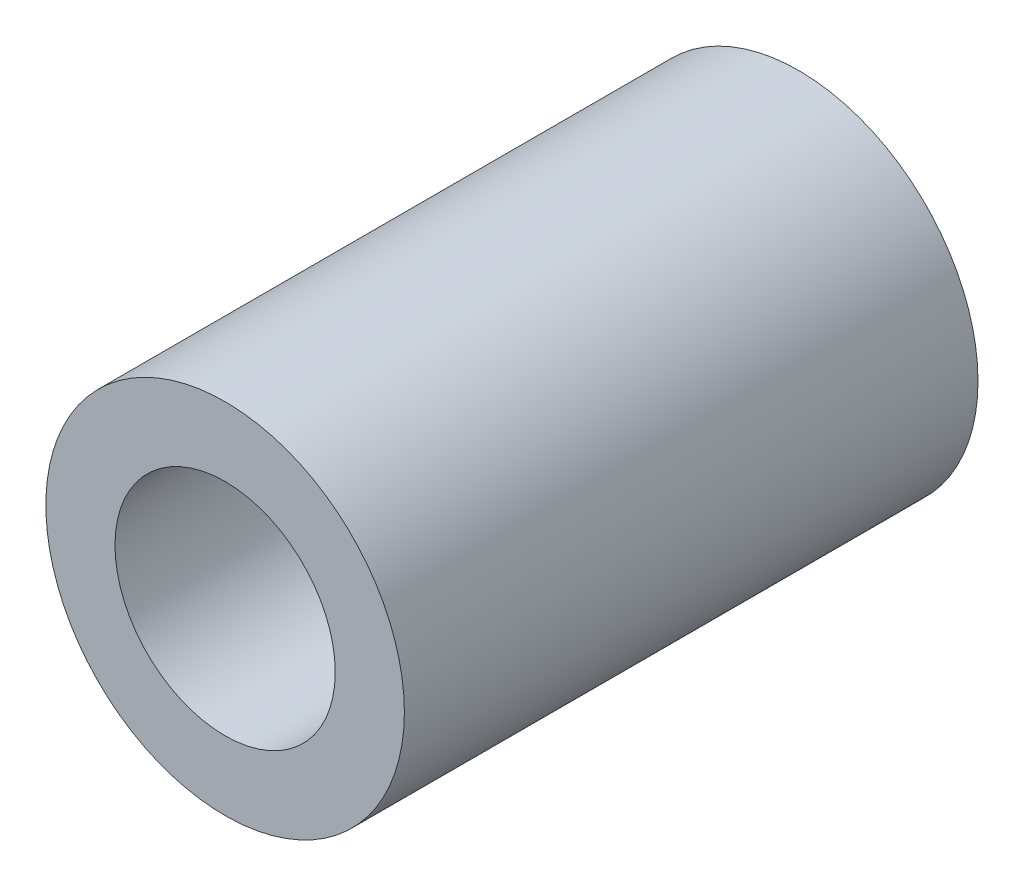
SolidWorks part; units mm, degrees
ref_plane "Front Plane" through (0, 0, 0) normal (0, 0, 1) x (1, 0, 0)
ref_plane "Top Plane" through (0, 0, 0) normal (0, 1, 0) x (1, 0, 0)
ref_plane "Right Plane" through (0, 0, 0) normal (1, 0, 0) x (0, 0, -1)
sketch "Sketch1" plane through (0, 0, 0) normal (0, 0, 1) x (1, 0, 0)
  line L0 (0, 2.4384) -> (0, 3.9688) construction
  line L1 (0, -2.4384) -> (0, -3.9688) construction
  circle A0 centre (0, 0) radius 3.9688
  circle A1 centre (0, 0) radius 2.4384
  dimension "OD" = 7.9375
  dimension "ID" = 4.8768
sketch "Sketch2" plane through (0, 0, 0) normal (1, 0, 0) x (0, 0, -1)
  line L0 (-6.35, 2.4384) -> (6.35, 2.4384) construction
  line L1 (-6.35, -2.4384) -> (6.35, -2.4384) construction
  line L2 (-6.35, -3.9688) -> (6.35, -3.9688) construction
  line L3 (-6.35, 3.9688) -> (6.35, 3.9688) construction
  dimension "Length" = 12.7
extrude "Extrude1" add sketch "Sketch1" along normal up to vertex (6.35 mm away) and the other way up to vertex (6.35 mm away) up to point (0, 2.4384, 6.35) other way up to point (0, 2.4384, -6.35)
sketch "Sketch3" plane through (0, 0, 6.35) normal (0, 0, 1) x (1, 0, 0)
  circle A0 centre (0, 0) radius 2.4384 construction
  circle A3 centre (0, 0) radius 2.4384
  point P3 (-2.4384, 0)
